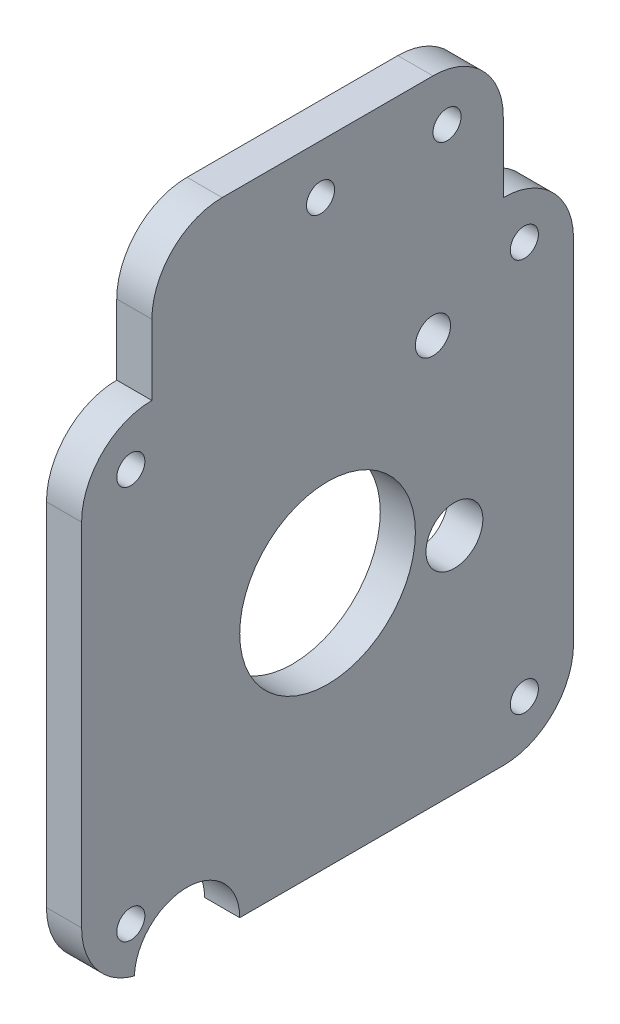
SolidWorks part; units mm, degrees
ref_plane "Alzado" through (0, 0, 0) normal (0, 0, 1) x (1, 0, 0)
ref_plane "Planta" through (0, 0, 0) normal (0, 1, 0) x (1, 0, 0)
ref_plane "Vista lateral" through (0, 0, 0) normal (1, 0, 0) x (0, 0, -1)
sketch "Croquis1" plane through (0, 0, 0) normal (1, 0, 0) x (0, 0, -1)
  line L0 (35, 70) -> (35, 35) construction
  line L1 (10, 0) -> (60, 0)
  line L2 (0, 10) -> (0, 60)
  line L3 (60, 70) -> (10, 70) construction
  line L4 (70, 10) -> (70, 60)
  line L5 (0, 35) -> (35, 35) construction
  line L8 (60, 70) -> (60, 80)
  line L9 (50, 90) -> (20, 90)
  line L10 (10, 70) -> (10, 80)
  arc A0 (10, 0) -> (0, 10) centre (10, 10) cw
  arc A1 (60, 0) -> (70, 10) centre (60, 10) ccw
  arc A2 (60, 70) -> (70, 60) centre (60, 60) cw
  arc A3 (0, 60) -> (10, 70) centre (10, 60) cw
  circle A4 centre (7, 63) radius 2
  circle A5 centre (63, 63) radius 2
  circle A6 centre (63, 7) radius 2
  circle A7 centre (7, 7) radius 2
  circle A8 centre (53.05, 31.84) radius 4.05
  arc A9 (20, 90) -> (10, 80) centre (20, 80) ccw
  arc A10 (60, 80) -> (50, 90) centre (50, 80) ccw
  circle A11 centre (35, 35) radius 12.5
  point P7 (0, 0)
  point P12 (70, 70)
  point P15 (0, 70)
  point P34 (60, 90)
  dimension "D3" = 10
  dimension "D4" = 4
  dimension "D7" = 8.1
  dimension "D9" = 10
  dimension "D11" = 25
  dimension "D1" = 70
  dimension "D2" = 70
  dimension "D5" = 35
  dimension "D6" = 7
  dimension "D8" = 20
  dimension "D10" = 35
  dimension "D12" = 35
  dimension "D13" = 16.95
  dimension "D14" = 31.84
extrude "Saliente-Extruir1" add sketch "Croquis1" along normal blind 5
sketch "Croquis2" plane through (5, 0, 0) normal (1, 0, 0) x (0, 0, -1)
  line L0 (60, 70) -> (10, 70) construction
  line L1 (52, 83) -> (34, 83) construction
  line L2 (10, 0) -> (60, 0) construction
  line L3 (0, 60) -> (0, 10) construction
  line L4 (35, 35) -> (35, 70) construction
  line L5 (60, 70) -> (60, 80) construction
  line L6 (0, 60) -> (0, 10) construction
  circle A0 centre (15, 0) radius 7.5
  circle A1 centre (50, 58) radius 2.5
  arc A2 (10, 70) -> (0, 60) centre (10, 60) ccw construction
  circle A3 centre (52, 83) radius 2
  circle A4 centre (34, 83) radius 2
  dimension "D1" = 15
  dimension "D3" = 5
  dimension "D5" = 23
  dimension "D6" = 4
  dimension "D7" = 4
  dimension "D2" = 15
  dimension "D4" = 15
  dimension "D8" = 18
  dimension "D9" = 8
  dimension "D10" = 13
  dimension "D11" = 35
extrude "Cortar-Extruir1" cut sketch "Croquis2" against normal blind 10
sketch "Croquis3" plane through (0, 0, 0) normal (-1, 0, 0) x (0, 0, 1)
  line L6 (0, 10) -> (0, 60)
  line L7 (-10, 70) -> (-10, 80)
  line L8 (-20, 90) -> (-50, 90)
  line L9 (-60, 80) -> (-60, 70)
  line L10 (-70, 60) -> (-70, 10)
  line L11 (-60, 0) -> (-22.5, 0)
  line L12 (0, 10) -> (0, 60)
  line L13 (-10, 70) -> (-10, 80)
  line L14 (-20, 90) -> (-50, 90)
  line L15 (-60, 80) -> (-60, 70)
  line L16 (-70, 60) -> (-70, 10)
  line L17 (-60, 0) -> (-22.5, 0)
  circle A0 centre (-34, 83) radius 2 construction
  circle A1 centre (-7, 63) radius 2 construction
  circle A2 centre (-7, 7) radius 2 construction
  circle A3 centre (-53.05, 31.84) radius 4.05 construction
  circle A4 centre (-63, 7) radius 2 construction
  circle A5 centre (-50, 58) radius 2.5 construction
  circle A6 centre (-63, 63) radius 2 construction
  arc A7 (-7.5067, 0.3158) -> (-22.5, 0) centre (-15, 0) ccw
  arc A8 (-7.5067, 0.3158) -> (0, 10) centre (-10, 10) ccw
  arc A9 (0, 60) -> (-10, 70) centre (-10, 60) ccw
  arc A10 (-10, 80) -> (-20, 90) centre (-20, 80) ccw
  arc A11 (-50, 90) -> (-60, 80) centre (-50, 80) ccw
  arc A12 (-60, 70) -> (-70, 60) centre (-60, 60) ccw
  arc A13 (-70, 10) -> (-60, 0) centre (-60, 10) ccw
  arc A14 (-7.5067, 0.3158) -> (-22.5, 0) centre (-15, 0) ccw
  arc A15 (-7.5067, 0.3158) -> (0, 10) centre (-10, 10) ccw
  arc A16 (0, 60) -> (-10, 70) centre (-10, 60) ccw
  arc A17 (-10, 80) -> (-20, 90) centre (-20, 80) ccw
  arc A18 (-50, 90) -> (-60, 80) centre (-50, 80) ccw
  arc A19 (-60, 70) -> (-70, 60) centre (-60, 60) ccw
  arc A20 (-70, 10) -> (-60, 0) centre (-60, 10) ccw
  circle A21 centre (-52, 83) radius 2 construction
  circle A22 centre (-34, 83) radius 2
  circle A23 centre (-7, 63) radius 2
  circle A24 centre (-7, 7) radius 2
  circle A25 centre (-35, 35) radius 12.5 construction
  circle A26 centre (-63, 7) radius 2
  circle A27 centre (-50, 58) radius 2.5
  circle A28 centre (-63, 63) radius 2
  circle A29 centre (-52, 83) radius 2
  circle A30 centre (-35, 35) radius 12.5
  circle A31 centre (-53.05, 31.84) radius 4.05
  dimension "D1" = 0
